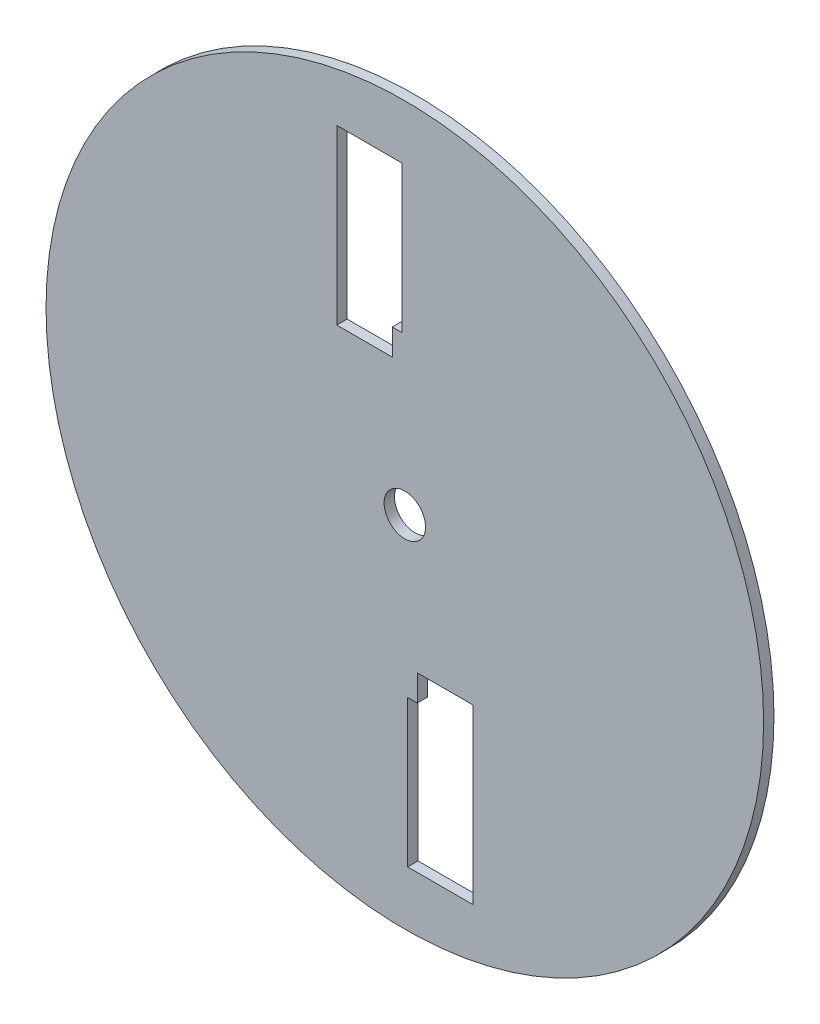
SolidWorks part; units mm, degrees
ref_plane "Front Plane" through (0, 0, 0) normal (0, 0, 1) x (1, 0, 0)
ref_plane "Top Plane" through (0, 0, 0) normal (0, 1, 0) x (1, 0, 0)
ref_plane "Right Plane" through (0, 0, 0) normal (1, 0, 0) x (0, 0, -1)
sketch "Sketch1" plane through (0, 0, 0) normal (0, 0, 1) x (1, 0, 0)
  line L0 (-6.35, 0) -> (-6.35, 42.8001) construction
  line L1 (-6.35, 40) -> (-3.85, 40)
  line L2 (-3.85, 40) -> (-3.85, 48)
  line L3 (-3.85, 48) -> (-0.85, 48)
  line L4 (-0.85, 48) -> (-0.85, 93)
  line L5 (-0.85, 93) -> (-20.85, 93)
  line L6 (-20.85, 93) -> (-20.85, 40)
  line L7 (-20.85, 40) -> (-18.35, 40)
  line L8 (-18.35, 40) -> (-6.35, 40)
  line L9 (-6.35, 40) -> (-6.35, 0)
  line L10 (6.35, -40) -> (3.85, -40)
  line L11 (3.85, -40) -> (3.85, -48)
  line L12 (3.85, -48) -> (0.85, -48)
  line L13 (0.85, -48) -> (0.85, -93)
  line L14 (0.85, -93) -> (20.85, -93)
  line L15 (20.85, -93) -> (20.85, -40)
  line L16 (20.85, -40) -> (18.35, -40)
  line L17 (18.35, -40) -> (6.35, -40)
  line L18 (-3.85, 40) -> (3.85, -40) construction
  circle A0 centre (0, 0) radius 110
  circle A1 centre (0, 0) radius 6.35
  point P14 (-6.35, 0)
  point P27 (0, 0)
  point P46 (0, 0)
  dimension "D5" = 12.7
  dimension "D11" = 220
  dimension "D1" = 17
  dimension "D2" = 12
  dimension "D3" = 53
  dimension "D4" = 45
  dimension "D6" = 20
  dimension "D7" = 40
  dimension "D8" = 2
extrude "Boss-Extrude1" add sketch "Sketch1" along normal mid plane 3.175
